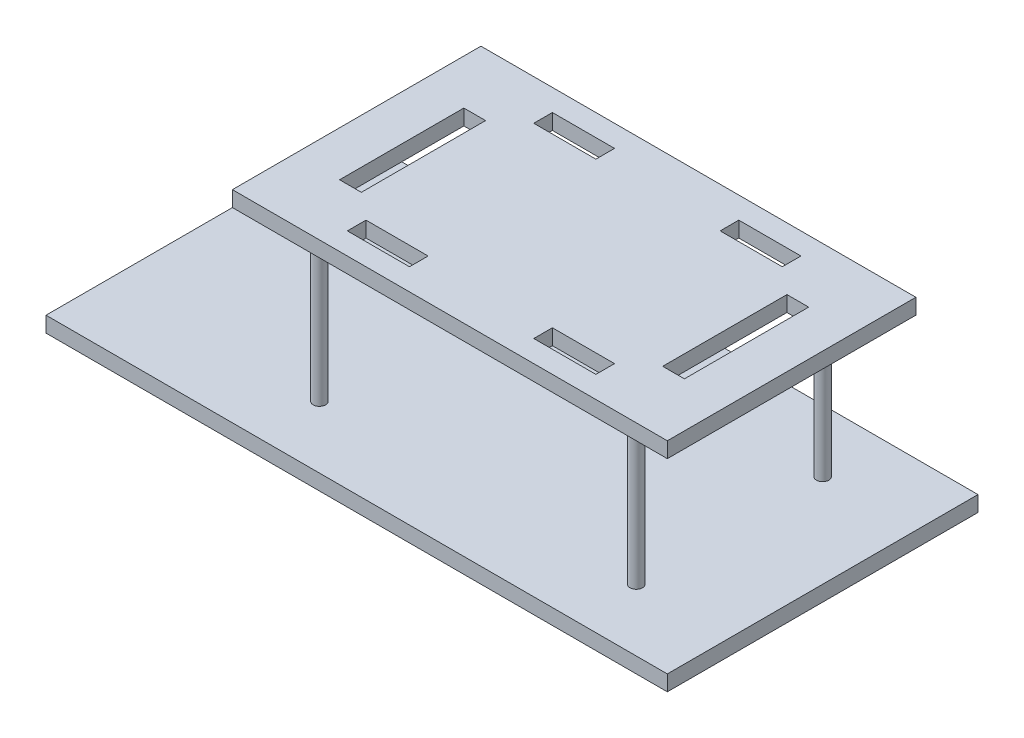
SolidWorks part; units mm, degrees
ref_plane "Front Plane" through (0, 0, 0) normal (0, 0, 1) x (1, 0, 0)
ref_plane "Top Plane" through (0, 0, 0) normal (0, 1, 0) x (1, 0, 0)
ref_plane "Right Plane" through (0, 0, 0) normal (1, 0, 0) x (0, 0, -1)
sketch "Sketch1" plane through (0, 0, 0) normal (0, 1, 0) x (1, 0, 0)
  line L1 (-100, 50) -> (100, 50)
  line L2 (-100, 50) -> (-100, -50)
  line L3 (-100, -50) -> (100, -50)
  line L4 (100, 50) -> (100, -50)
  line L5 (-100, 50) -> (100, -50) construction
  line L6 (-100, -50) -> (100, 50) construction
  point P0 (0, 0)
  dimension "D1" = 200
  dimension "D2" = 100
extrude "Boss-Extrude2" add sketch "Sketch1" along normal blind 5
sketch "Sketch2" plane through (0, 5, 0) normal (0, 1, 0) x (1, 0, 0)
  line L0 (0, 50) -> (0, -50) construction
  line L1 (100, 50) -> (-100, 50) construction
  line L2 (-100, -50) -> (100, -50) construction
  line L3 (-100, 0) -> (100, 0) construction
  line L4 (-100, 50) -> (-100, -50) construction
  line L5 (100, -50) -> (100, 50) construction
  circle A0 centre (70, -30) radius 2
  circle A1 centre (-32, -30) radius 2
  circle A2 centre (70, 30) radius 2
  circle A3 centre (-32, 30) radius 2
  dimension "D1" = 4
  dimension "D4" = 4
  dimension "D2" = 30
  dimension "D3" = 70
  dimension "D5" = 32
  dimension "D6" = 30
extrude "Boss-Extrude3" add sketch "Sketch2" along normal blind 50
sketch "Sketch3" plane through (0, 55, 0) normal (0, 1, 0) x (1, 0, 0)
  line L0 (100, -50) -> (100, 50) construction
  line L1 (-50, 40) -> (90, 40)
  line L2 (-50, 40) -> (-50, -40)
  line L3 (-50, -40) -> (90, -40)
  line L4 (90, 40) -> (90, -40)
  line L5 (-50, 40) -> (90, -40) construction
  line L6 (-50, -40) -> (90, 40) construction
  line L7 (-100, 50) -> (-100, -50) construction
  point P0 (20, 0)
  point P8 (2.7352, -45.8443)
  dimension "D1" = 40
  dimension "D2" = 40
  dimension "D3" = 10
  dimension "D4" = 50
extrude "Boss-Extrude4" add sketch "Sketch3" along normal blind 5
sketch "Sketch4" plane through (0, 60, 0) normal (0, 1, 0) x (1, 0, 0)
  line L0 (20, 40) -> (20, -40) construction
  line L1 (90, 40) -> (-50, 40) construction
  line L2 (-50, -40) -> (90, -40) construction
  line L3 (90, 0) -> (-50, 0) construction
  line L4 (90, -40) -> (90, 40) construction
  line L5 (-50, 40) -> (-50, -40) construction
  line L6 (-20, 27) -> (-20, 33)
  line L7 (-20, -27) -> (0, -27)
  line L8 (-20, -27) -> (-20, -33)
  line L9 (-20, -33) -> (0, -33)
  line L10 (0, -27) -> (0, -33)
  line L11 (0, 27) -> (0, 33)
  line L12 (-20, 33) -> (0, 33)
  line L13 (-20, 27) -> (0, 27)
  line L14 (40, -27) -> (40, -33)
  line L15 (60, -33) -> (40, -33)
  line L16 (60, -27) -> (60, -33)
  line L17 (60, -27) -> (40, -27)
  line L18 (60, 27) -> (40, 27)
  line L19 (60, 33) -> (40, 33)
  line L20 (40, 27) -> (40, 33)
  line L21 (60, 27) -> (60, 33)
  dimension "D1" = 7
  dimension "D2" = 20
  dimension "D3" = 6
  dimension "D4" = 20
extrude "Cut-Extrude1" cut sketch "Sketch4" against normal blind 5
sketch "Sketch7" plane through (0, 60, 0) normal (0, 1, 0) x (1, 0, 0)
  line L0 (-100, 0) -> (100, 0) construction
  line L1 (-28.5, 20) -> (-35.5, 20)
  line L2 (-28.5, 20) -> (-28.5, -20)
  line L3 (-28.5, -20) -> (-35.5, -20)
  line L4 (-35.5, 20) -> (-35.5, -20)
  line L5 (-28.5, 20) -> (-35.5, -20) construction
  line L6 (-28.5, -20) -> (-35.5, 20) construction
  line L8 (20, 40) -> (20, -40) construction
  line L9 (90, 40) -> (-50, 40) construction
  line L10 (-50, -40) -> (90, -40) construction
  line L11 (-50.2863, 0) -> (89.6316, 0) construction
  line L12 (68.5, -20) -> (75.5, -20)
  line L13 (75.5, 20) -> (75.5, -20)
  line L14 (68.5, 20) -> (68.5, -20)
  line L15 (68.5, 20) -> (75.5, 20)
  point P0 (-32, 0)
  dimension "D1" = 7
  dimension "D2" = 40
  dimension "D3" = 48.5
extrude "Cut-Extrude2" cut sketch "Sketch7" against normal blind 5
